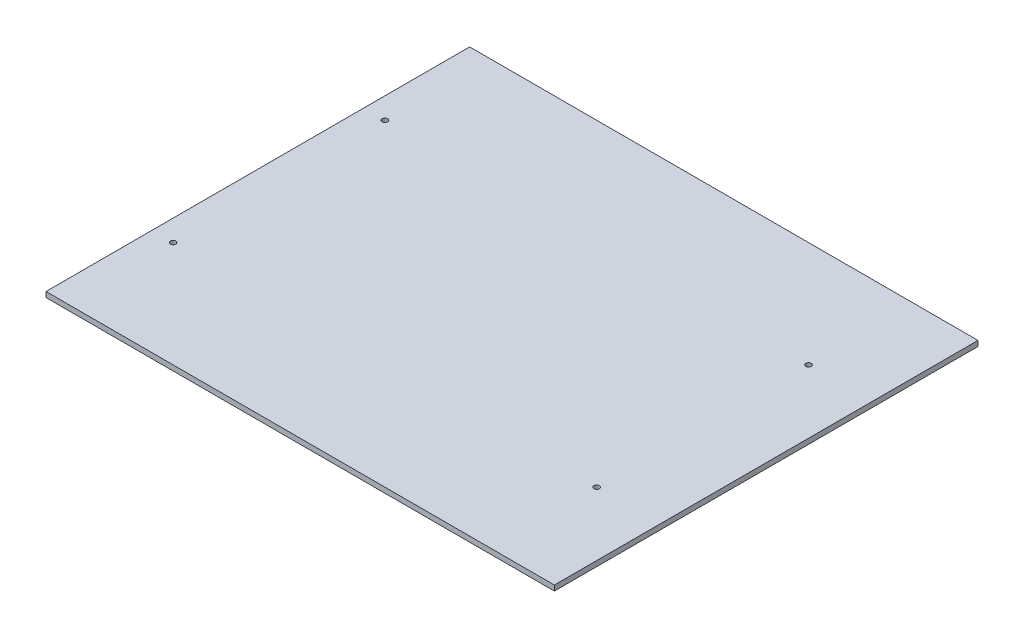
SolidWorks part; units mm, degrees
material "AISI 1020"
ref_plane "Front Plane" through (0, 0, 0) normal (0, 0, 1) x (1, 0, 0)
ref_plane "Top Plane" through (0, 0, 0) normal (0, 1, 0) x (1, 0, 0)
ref_plane "Right Plane" through (0, 0, 0) normal (1, 0, 0) x (0, 0, -1)
sketch "Sketch1" plane through (0, 0, 0) normal (0, 1, 0) x (1, 0, 0)
  line L1 (0, 0) -> (-609.6, 0)
  line L2 (0, 0) -> (0, 508)
  line L3 (0, 508) -> (-609.6, 508)
  line L4 (-609.6, 0) -> (-609.6, 508)
  dimension "D1" = 609.6
  dimension "D2" = 508
extrude "Boss-Extrude1" add sketch "Sketch1" along normal blind 6.35
hole_wizard "1/4 Clearance Hole1" positions "Sketch2" profile "Sketch3" hole size "1/4" standard "ANSI Inch"
sketch "Sketch2" plane through (0, 6.35, 0) normal (0, 1, 0) x (1, 0, 0)
  line L0 (-584.2, 381) -> (-76.2, 381) construction
  line L1 (-76.2, 381) -> (-76.2, 127) construction
  line L2 (-76.2, 127) -> (-584.2, 127) construction
  line L3 (-584.2, 127) -> (-584.2, 381) construction
  line L5 (-609.6, 508) -> (-609.6, 0) construction
  line L6 (0, 0) -> (0, 508) construction
  line L11 (-609.6, 254) -> (-584.2, 254) construction
  point P0 (-76.2, 381)
  point P2 (-76.2, 127)
  point P4 (-584.2, 127)
  point P6 (-584.2, 381)
  dimension "D1" = 25.4
  dimension "D2" = 76.2
  dimension "D3" = 254
sketch "Sketch3" plane through (-76.2, 6.35, -381) normal (1, 0, 0) x (0, 0, 1)
  line L0 (0, 0) -> (0, 24.3131)
  line L1 (0, 24.3131) -> (3.2639, 22.352)
  line L2 (3.2639, 22.352) -> (3.2639, 0)
  line L5 (3.2639, 0) -> (0, 0)
  line L10 (0, 24.3131) -> (-3.2639, 22.352) construction
  line L11 (0, -6.35) -> (0, 107.95) construction
  dimension "Hole Dia." = 6.5278
  dimension "Hole Depth" = 22.352
  dimension "Drill Angle" = 118
